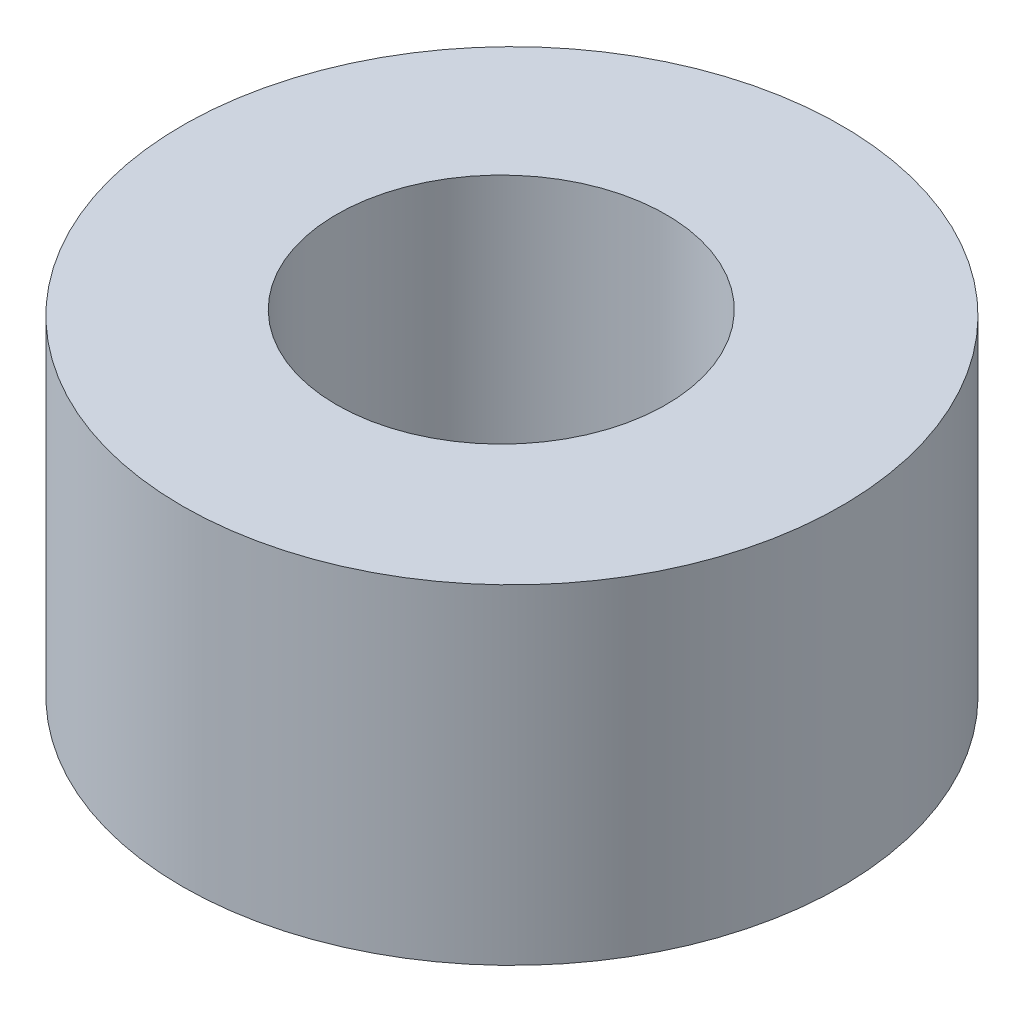
SolidWorks part; units mm, degrees
ref_plane "Front Plane" through (0, 0, 0) normal (0, 0, 1) x (1, 0, 0)
ref_plane "Top Plane" through (0, 0, 0) normal (0, 1, 0) x (1, 0, 0)
ref_plane "Right Plane" through (0, 0, 0) normal (1, 0, 0) x (0, 0, -1)
sketch "Sketch1" plane through (0, 0, 0) normal (0, 1, 0) x (1, 0, 0)
  circle A0 centre (0, 0) radius 12.7
  circle A1 centre (-0.4116, 0) radius 6.35
  dimension "D1" = 12.7
  dimension "D2" = 25.4
extrude "Boss-Extrude1" add sketch "Sketch1" along normal blind 12.7
